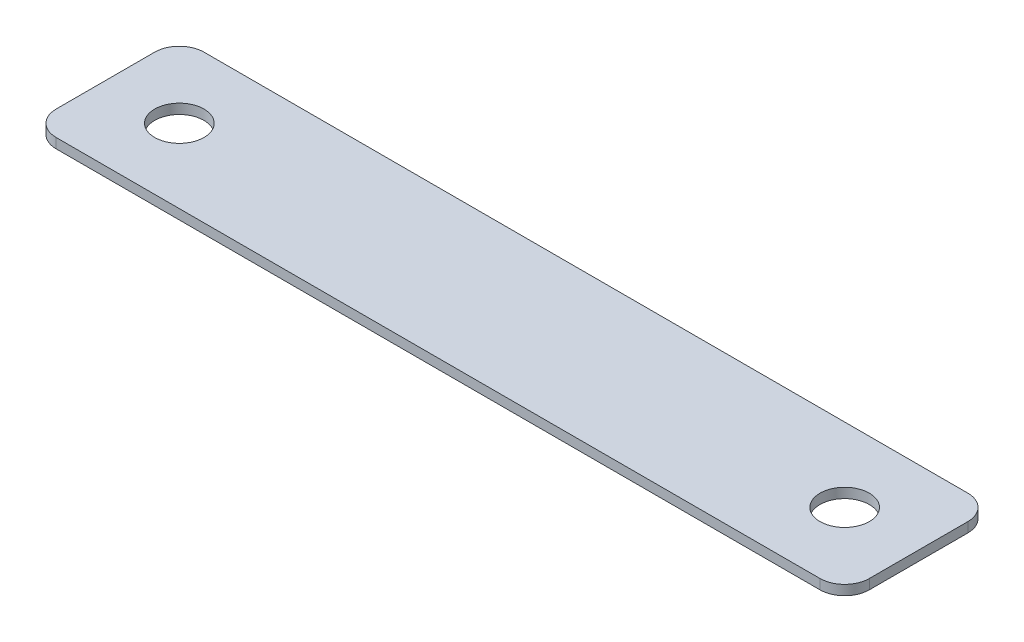
SolidWorks part; units mm, degrees
ref_plane "Front" through (0, 0, 0) normal (0, 0, 1) x (1, 0, 0)
ref_plane "Top" through (0, 0, 0) normal (0, 1, 0) x (1, 0, 0)
ref_plane "Right" through (0, 0, 0) normal (1, 0, 0) x (0, 0, -1)
sketch "Sketch1" plane through (0, 0, 0) normal (0, 1, 0) x (1, 0, 0)
  line L0 (0, 19.05) -> (19.05, 19.05) construction
  line L1 (6.35, 0) -> (203.2, 0)
  line L2 (0, 6.35) -> (0, 31.75)
  line L3 (6.35, 38.1) -> (203.2, 38.1)
  line L5 (190.5, 19.05) -> (209.55, 19.05) construction
  line L6 (209.55, 31.75) -> (209.55, 6.35)
  circle A0 centre (19.05, 19.05) radius 6.35
  circle A4 centre (190.5, 19.05) radius 6.35
  arc A7 (0, 31.75) -> (6.35, 38.1) centre (6.35, 31.75) cw
  arc A8 (6.35, 0) -> (0, 6.35) centre (6.35, 6.35) cw
  arc A9 (209.55, 6.35) -> (203.2, 0) centre (203.2, 6.35) cw
  arc A10 (209.55, 31.75) -> (203.2, 38.1) centre (203.2, 31.75) ccw
  point P23 (0, 38.1)
  point P26 (0, 0)
  dimension "D4" = 12.7
  dimension "D5" = 19.05
  dimension "D6" = 12.7
  dimension "D7" = 6.35
  dimension "D1" = 38.1
  dimension "D2" = 171.45
  dimension "D3" = 19.05
extrude "Boss-Extrude1" add sketch "Sketch1" along normal blind 2.54
